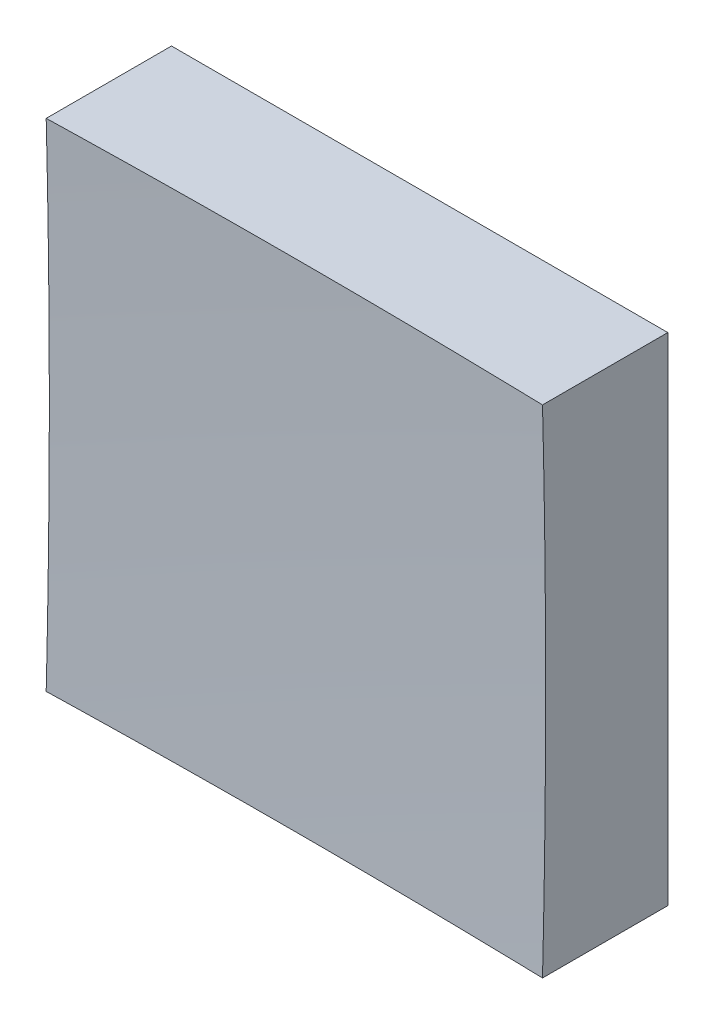
SolidWorks part; units mm, degrees
ref_plane "前视基准面" through (0, 0, 0) normal (0, 0, 1) x (1, 0, 0)
ref_plane "上视基准面" through (0, 0, 0) normal (0, 1, 0) x (1, 0, 0)
ref_plane "右视基准面" through (0, 0, 0) normal (1, 0, 0) x (0, 0, -1)
sketch "草图1" plane through (0, 0, 0) normal (0, 0, 1) x (1, 0, 0)
  line L1 (-12.5, 12.5) -> (12.5, 12.5)
  line L2 (-12.5, 12.5) -> (-12.5, -12.5)
  line L3 (-12.5, -12.5) -> (12.5, -12.5)
  line L4 (12.5, 12.5) -> (12.5, -12.5)
  line L5 (-12.5, 12.5) -> (12.5, -12.5) construction
  line L6 (-12.5, -12.5) -> (12.5, 12.5) construction
  point P0 (0, 0)
  dimension "D1" = 25
  dimension "D2" = 25
extrude "凸台-拉伸1" add sketch "草图1" along normal blind 20 contours L2 L3 L4 L1
sketch "草图2" plane through (0, 0, 0) normal (0, 1, 0) x (1, 0, 0)
  line L0 (-7.4603, -6) -> (7.3192, -6) construction
  line L1 (0, 0) -> (0, -12.1749) construction
  line L2 (487.4227, -394.5591) -> (0, -394.5591)
  line L3 (0, -394.5591) -> (0, -6)
  arc A1 (487.4227, -394.5591) -> (0, -6) centre (0, -506) ccw
  dimension "D2" = 1000
  dimension "D1" = 6
revolve "切除-旋转2" cut sketch "草图2" angle 360 about L3
